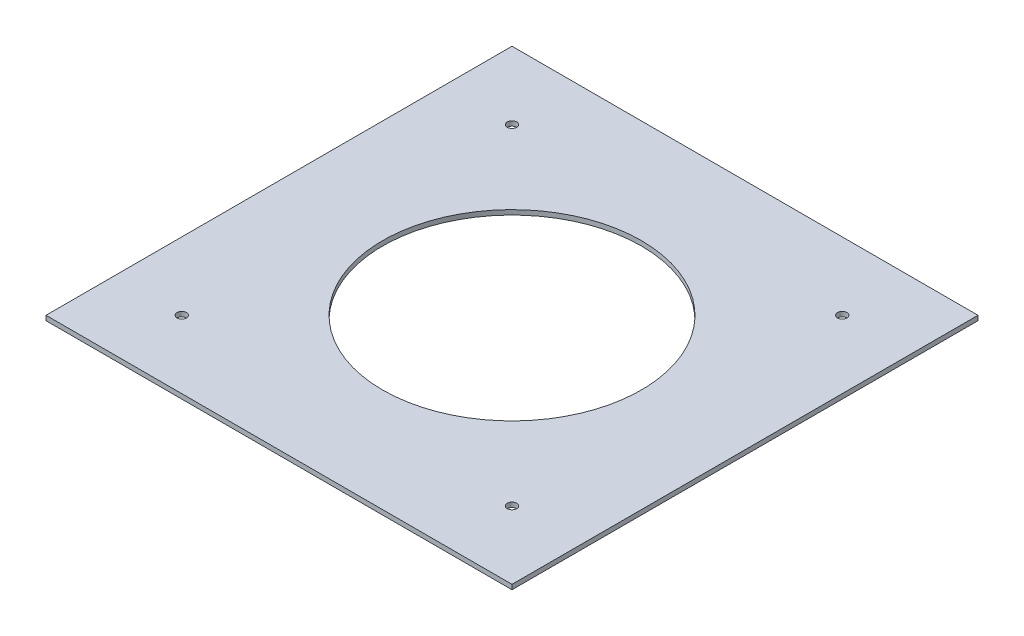
SolidWorks part; units mm, degrees
material "1023 Carbon Steel Sheet (SS)"
ref_plane "Front Plane" through (0, 0, 0) normal (0, 0, 1) x (1, 0, 0)
ref_plane "Top Plane" through (0, 0, 0) normal (0, 1, 0) x (1, 0, 0)
ref_plane "Right Plane" through (0, 0, 0) normal (1, 0, 0) x (0, 0, -1)
sketch "Sketch1" plane through (0, 0, 0) normal (0, 1, 0) x (1, 0, 0)
  line L1 (-49.3914, -49.3914) -> (49.3914, -49.3914)
  line L2 (-49.3914, -49.3914) -> (-49.3914, 49.3914)
  line L3 (-49.3914, 49.3914) -> (49.3914, 49.3914)
  line L4 (49.3914, -49.3914) -> (49.3914, 49.3914)
  line L5 (-49.3914, -49.3914) -> (49.3914, 49.3914) construction
  line L6 (-49.3914, 49.3914) -> (49.3914, -49.3914) construction
  point P0 (0, 0)
  dimension "D1" = 139.7
extrude "Boss-Extrude1" add sketch "Sketch1" along normal blind 1
sketch "Sketch3" plane through (0, 0, 0) normal (0, 1, 0) x (1, 0, 0)
  line L0 (-49.3914, -49.3914) -> (49.3914, 49.3914) construction
  line L1 (-35.0018, 35.0018) -> (35.0018, -35.0018) construction
  circle A0 centre (35.0018, 35.0018) radius 1
  circle A1 centre (35.0018, -35.0018) radius 1
  circle A2 centre (-35.0018, -35.0018) radius 1
  circle A3 centre (-35.0018, 35.0018) radius 1
  point P15 (0, 0)
  dimension "D3" = 2
  dimension "D2" = 99
  dimension "D1" = 4
extrude "Cut-Extrude2" cut sketch "Sketch3" along normal through all
sketch "Sketch8" plane through (0, 0, 0) normal (0, 1, 0) x (1, 0, 0)
  circle A0 centre (0, 0) radius 27.432 construction
  circle A1 centre (0, 0) radius 27.432
extrude "Cut-Extrude9" cut sketch "Sketch8" along normal through all
equation "\"D1@Boss-Extrude1\"=1mm"
equation "\"D3@Sketch3\"=2mm"
equation "\"D2@Sketch3\"=99mm"
